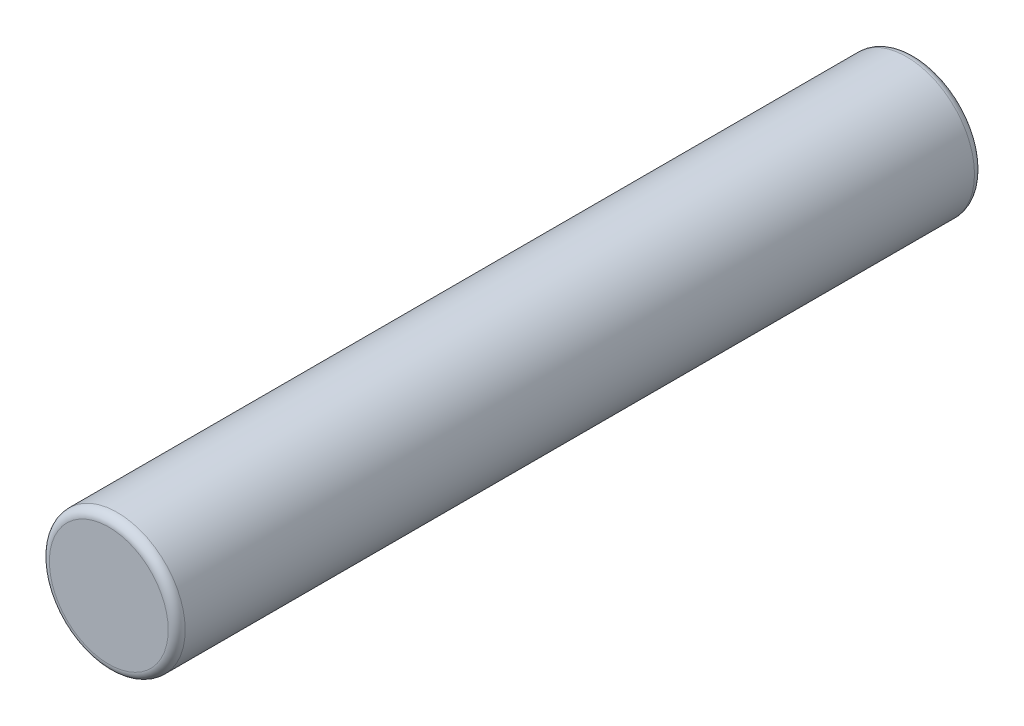
SolidWorks part; units mm, degrees
ref_plane "Front Plane" through (0, 0, 0) normal (0, 0, 1) x (1, 0, 0)
ref_plane "Top Plane" through (0, 0, 0) normal (0, 1, 0) x (1, 0, 0)
ref_plane "Right Plane" through (0, 0, 0) normal (1, 0, 0) x (0, 0, -1)
sketch "Sketch1" plane through (0, 0, 0) normal (0, 0, 1) x (1, 0, 0)
  circle A0 centre (0, 0) radius 0.8
  dimension "D1" = 1.6
extrude "Boss-Extrude1" add sketch "Sketch1" along normal blind 9.5
fillet "Fillet1" radius 0.1 2 edges at (0.8, 0, 0) (0.8, 0, 9.5)
